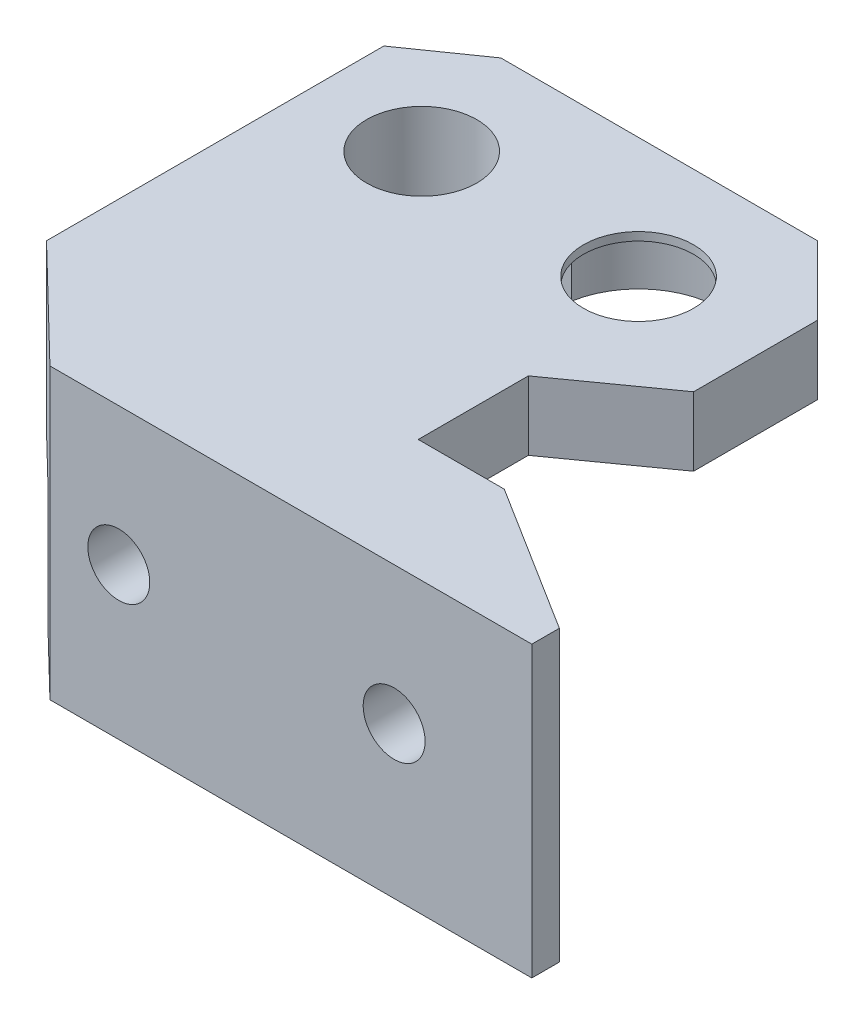
SolidWorks part; units mm, degrees
ref_plane "Front Plane" through (0, 0, 0) normal (0, 0, 1) x (1, 0, 0)
ref_plane "Top Plane" through (0, 0, 0) normal (0, 1, 0) x (1, 0, 0)
ref_plane "Right Plane" through (0, 0, 0) normal (1, 0, 0) x (0, 0, -1)
sketch "Sketch1" plane through (0, 0, 0) normal (0, 1, 0) x (1, 0, 0)
  line L0 (0, 0) -> (15.75, 0) construction
  line L5 (-4.25, 8.75) -> (18.75, 8.75)
  line L6 (18.75, 8.75) -> (23.75, 5.25)
  line L7 (23.75, 5.25) -> (23.75, -19.25)
  line L8 (23.75, -19.25) -> (15.75, -27)
  line L9 (15.75, -27) -> (-19.25, -27)
  line L10 (-19.25, -27) -> (-19.25, -25)
  line L11 (-19.25, -25) -> (-8.5, -18.25)
  line L12 (-8.5, -18.25) -> (-2.25, -18.25)
  line L13 (-2.25, -18.25) -> (-2.25, -10.25)
  line L14 (-2.25, -10.25) -> (-9.25, -5.25)
  line L15 (-9.25, -5.25) -> (-9.25, 3.75)
  line L16 (-9.25, 3.75) -> (-4.25, 8.75)
  line L17 (15.75, 0) -> (23.75, 0) construction
  circle A0 centre (0, 0) radius 4
  circle A1 centre (15.75, 0) radius 4
  point P0 (0, 0)
  dimension "D2" = 8
  dimension "D3" = 8
  dimension "D1" = 15.75
  dimension "D4" = 23
  dimension "D5" = 5
  dimension "D6" = 3.5
  dimension "D7" = 24.5
  dimension "D8" = 8
  dimension "D9" = 8.75
  dimension "D10" = 5
  dimension "D11" = 5
  dimension "D12" = 7
  dimension "D13" = 5
  dimension "D14" = 9
  dimension "D15" = 8
  dimension "D16" = 7.75
  dimension "D17" = 35
  dimension "D18" = 6.25
  dimension "D19" = 6.75
  dimension "D20" = 2
extrude "Boss-Extrude1" add sketch "Sketch1" along normal blind 5
sketch "Sketch2" plane through (0, 0, 0) normal (0, -1, 0) x (1, 0, 0)
  line L0 (23.75, 19.25) -> (23.75, -5.25)
  line L1 (23.75, -5.25) -> (20.25, -5.25)
  line L2 (20.25, -5.25) -> (20.25, 18.25)
  line L3 (20.25, 18.25) -> (-8.5, 18.25)
  line L4 (-8.5, 18.25) -> (-14.8704, 22.25)
  line L5 (-8.5, 18.25) -> (-19.25, 25) construction
  line L6 (-14.8704, 22.25) -> (20.6532, 22.25)
  line L7 (15.75, 27) -> (23.75, 19.25) construction
  line L8 (20.6532, 22.25) -> (23.75, 19.25)
  dimension "D1" = 3.5
  dimension "D2" = 4
extrude "Boss-Extrude2" add sketch "Sketch2" along normal blind 7
sketch "Sketch3" plane through (0, 0, 0) normal (0, -1, 0) x (1, 0, 0)
  line L5 (-14.8704, 22.25) -> (20.6532, 22.25)
  line L6 (20.6532, 22.25) -> (15.75, 27)
  line L7 (15.75, 27) -> (-19.25, 27)
  line L8 (-19.25, 27) -> (-19.25, 25)
  line L9 (-19.25, 25) -> (-14.8704, 22.25)
  line L10 (-14.8704, 22.25) -> (20.6532, 22.25)
  line L11 (20.6532, 22.25) -> (15.75, 27)
  line L12 (15.75, 27) -> (-19.25, 27)
  line L13 (-19.25, 27) -> (-19.25, 25)
  line L14 (-19.25, 25) -> (-14.8704, 22.25)
  dimension "D1" = 0
extrude "Boss-Extrude3" add sketch "Sketch3" along normal blind 16
sketch "Sketch6" plane through (0, 0, 0) normal (0, -1, 0) x (1, 0, 0)
  circle A0 centre (15.75, 0) radius 7
  circle A1 centre (15.75, 0) radius 4
  dimension "D1" = 14
extrude "Boss-Extrude4" add sketch "Sketch6" along normal blind 2.5
sketch "Sketch4" plane through (0, 0, 0) normal (0, -1, 0) x (1, 0, 0)
  line L0 (0, 0) -> (12.25, 0) construction
  line L1 (5.8838, -1) -> (12.3959, -1)
  line L2 (5.8838, 1) -> (12.3959, 1)
  line L3 (0, -1) -> (15.75, -1) construction
  line L4 (0, 1) -> (15.75, 1) construction
  line L5 (0, 0) -> (15.75, 0) construction
  arc A0 (5.8838, 1) -> (5.8838, -1) centre (0, 0) ccw
  arc A2 (12.3959, 1) -> (12.3959, -1) centre (15.75, 0) ccw
  dimension "D1" = 1
  dimension "D2" = 1
extrude "Cut-Extrude1" cut sketch "Sketch4" against normal blind 4.4
sketch "Sketch7" plane through (0, 4.4, 0) normal (0, -1, 0) x (1, 0, 0)
  line L2 (5.8838, -1) -> (11.877, -1)
  line L3 (11.877, 1) -> (5.8838, 1)
  line L4 (5.8838, -1) -> (11.877, -1)
  line L5 (11.877, 1) -> (5.8838, 1)
  arc A2 (5.8838, 1) -> (5.8838, -1) centre (0, 0) ccw
  arc A3 (11.877, 1) -> (11.877, -1) centre (15.75, 0) ccw
  arc A4 (5.8838, 1) -> (5.8838, -1) centre (0, 0) ccw
  arc A5 (11.877, 1) -> (11.877, -1) centre (15.75, 0) ccw
  dimension "D1" = 0
extrude "Cut-Extrude2" cut sketch "Sketch7" along normal through all
sketch "Sketch8" plane through (0, 0, 27) normal (0, 0, 1) x (1, 0, 0)
  line L0 (10.75, -5) -> (-9.25, -5) construction
  line L1 (-19.25, 5) -> (15.75, 5) construction
  line L2 (-19.25, 5) -> (-19.25, -16) construction
  circle A0 centre (10.75, -5) radius 2.25
  circle A1 centre (-9.25, -5) radius 2.25
  dimension "D1" = 4.5
  dimension "D2" = 4.5
  dimension "D3" = 20
  dimension "D4" = 10
  dimension "D5" = 10
extrude "Cut-Extrude3" cut sketch "Sketch8" against normal through all
sketch "Sketch9" plane through (0, 0, 18.25) normal (0, 0, -1) x (-1, 0, 0)
  circle A0 centre (-10.75, -5) radius 4
  circle A1 centre (9.25, -5) radius 4
  dimension "D1" = 8
  dimension "D2" = 8
extrude "Cut-Extrude4" cut sketch "Sketch9" against normal blind 4
mirror "Mirror1" about plane through (-19.25, 5, 27) normal (1, 0, 0) of "Boss-Extrude2", "Boss-Extrude4", "Cut-Extrude2", "Cut-Extrude3", "Cut-Extrude1", "Boss-Extrude3", "Boss-Extrude1", "Cut-Extrude4"
sketch "Sketch10" plane through (0, 5, 0) normal (0, 1, 0) x (1, 0, 0)
  line L0 (18.75, 8.75) -> (-4.25, 8.75) construction
  line L1 (30.4721, -27) -> (-19.25, -27)
  line L2 (30.4721, -27) -> (30.4721, 8.75)
  line L3 (30.4721, 8.75) -> (-19.25, 8.75)
  line L4 (-19.25, -27) -> (-19.25, 8.75)
  line L5 (30.4721, -27) -> (-19.25, 8.75) construction
  line L6 (30.4721, 8.75) -> (-19.25, -27) construction
  line L7 (15.75, -27) -> (-54.25, -27) construction
  point P0 (5.611, -9.125)
extrude "Cut-Extrude5" cut sketch "Sketch10" against normal through all
